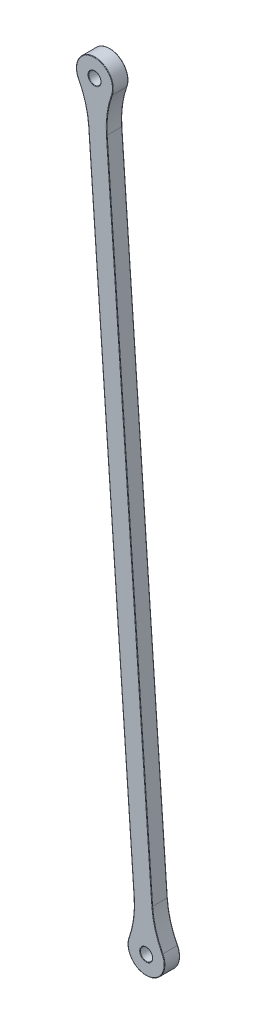
SolidWorks part; units mm, degrees
ref_plane "Front Plane" through (0, 0, 0) normal (0, 0, 1) x (1, 0, 0)
ref_plane "Top Plane" through (0, 0, 0) normal (0, 1, 0) x (1, 0, 0)
ref_plane "Right Plane" through (0, 0, 0) normal (1, 0, 0) x (0, 0, -1)
sketch "Sketch1" plane through (0, 0, 0) normal (0, 0, 1) x (1, 0, 0)
  line L0 (16.1627, 287.9649) -> (33.021, 48.5577) construction
  line L1 (16.1627, 287.9649) -> (33.021, 48.5577) construction
  line L2 (33.021, 48.5577) -> (16.1627, 287.9649) construction
  line L3 (30.0284, 48.347) -> (13.1701, 287.7542)
  line L4 (36.0135, 48.7685) -> (19.1553, 288.1757)
  circle A0 centre (16.1627, 287.9649) radius 6
  circle A1 centre (33.021, 48.5577) radius 6
  arc A2 (30.0284, 48.347) -> (36.0135, 48.7685) centre (33.021, 48.5577) ccw
  arc A3 (19.1553, 288.1757) -> (13.1701, 287.7542) centre (16.1627, 287.9649) ccw
  arc A4 (13.1701, 287.7542) -> (19.1553, 288.1757) centre (16.1627, 287.9649) ccw
  arc A5 (36.0135, 48.7685) -> (30.0284, 48.347) centre (33.021, 48.5577) ccw
  circle A6 centre (16.1627, 287.9649) radius 2
  circle A7 centre (33.021, 48.5577) radius 2
  point P5 (24.5918, 168.2613)
  dimension "D1" = 12
  dimension "D3" = 4
  dimension "D4" = 4
  dimension "D2" = 6
extrude "Boss-Extrude1" add sketch "Sketch1" against normal blind 5 contours A1 L4 A0 L3 | A4 L3 A0 L4 | A3 L4 A0 L3 | A3 A4 A6 | A2 A5 A7 | A2 L3 A1 L4 | A5 L4 A1 L3
fillet "Fillet1" radius 30 4 edges at (19.5203, 282.9923, -2.5) (13.5351, 282.5709, -2.5) (29.6634, 53.5303, -2.5) (35.6485, 53.9518, -2.5)
fillet "Fillet3" radius 0.15 20 edges at (35.021, 48.5577, -5) (35.021, 48.5577, 0) (18.1627, 287.9649, -5) (18.1627, 287.9649, 0) (36.0632, 57.0562, -5) (36.0632, 57.0562, 0) (27.5844, 168.4721, -5) (27.5844, 168.4721, 0) (20.3658, 279.9767, -5) (20.3658, 279.9767, 0) (15.7412, 293.9501, 0) (15.7412, 293.9501, -5) (13.1205, 279.4665, -5) (13.1205, 279.4665, 0) (21.5992, 168.0506, 0) (21.5992, 168.0506, -5) (28.8178, 56.546, -5) (28.8178, 56.546, 0) (33.4424, 42.5726, 0) (33.4424, 42.5726, -5)
